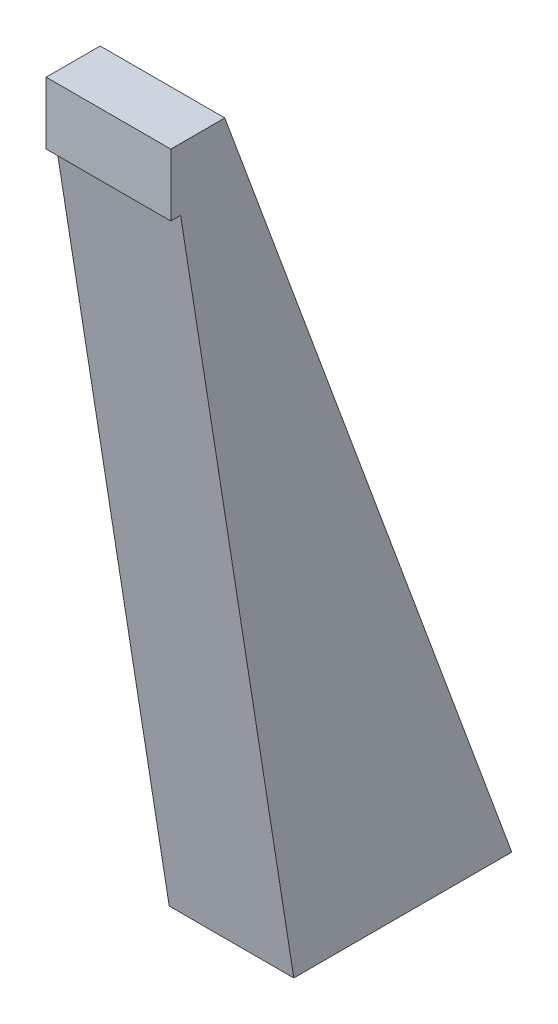
SolidWorks part; units mm, degrees
ref_plane "Front Plane" through (0, 0, 0) normal (0, 0, 1) x (1, 0, 0)
ref_plane "Top Plane" through (0, 0, 0) normal (0, 1, 0) x (1, 0, 0)
ref_plane "Right Plane" through (0, 0, 0) normal (1, 0, 0) x (0, 0, -1)
sketch "Sketch1" plane through (0, 0, 0) normal (1, 0, 0) x (0, 0, -1)
  line L0 (0, 0) -> (-59.2342, 375.3549)
  line L1 (-59.2342, 375.3549) -> (-33.2342, 375.3549)
  line L2 (-33.2342, 375.3549) -> (105, 0)
  line L3 (105, 0) -> (0, 0)
  dimension "D1" = 380
  dimension "D2" = 400
  dimension "D3" = 105
  dimension "D4" = 26
extrude "Boss-Extrude1" add sketch "Sketch1" along normal blind 60
sketch "Sketch2" plane through (0, 0, 0) normal (-1, 0, 0) x (0, 0, 1)
  line L1 (33.2342, 375.3549) -> (59.2342, 375.3549)
  line L2 (33.2342, 375.3549) -> (33.2342, 345.3549)
  line L3 (33.2342, 345.3549) -> (59.2342, 345.3549)
  line L4 (59.2342, 375.3549) -> (59.2342, 345.3549)
  point P5 (0, 0)
  dimension "D1" = 30
extrude "Boss-Extrude2" add sketch "Sketch2" against normal blind 60
